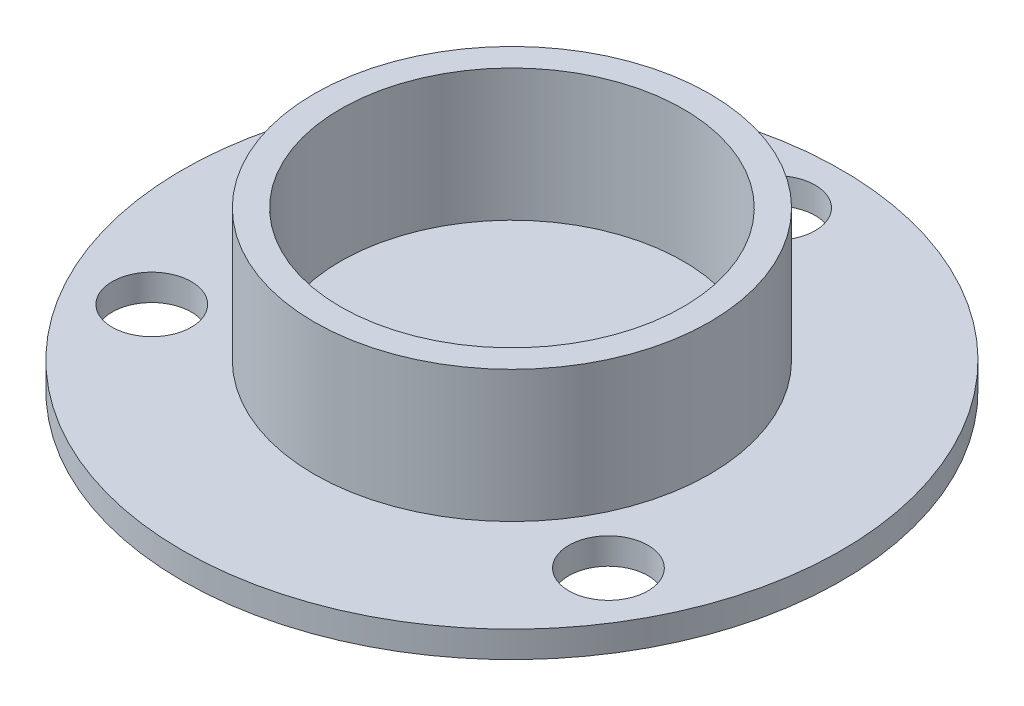
SolidWorks part; units mm, degrees
ref_plane "Front Plane" through (0, 0, 0) normal (0, 0, 1) x (1, 0, 0)
ref_plane "Top Plane" through (0, 0, 0) normal (0, 1, 0) x (1, 0, 0)
ref_plane "Right Plane" through (0, 0, 0) normal (1, 0, 0) x (0, 0, -1)
sketch "Sketch2" plane through (0, 0, 0) normal (0, 1, 0) x (1, 0, 0)
  circle A0 centre (0, 0) radius 12.5
  circle A3 centre (0, 10) radius 1.5
  circle A4 centre (8.6603, -5) radius 1.5
  circle A5 centre (-8.6603, -5) radius 1.5
  point P14 (0, 0)
  dimension "D1" = 3
  dimension "D2" = 3
extrude "Boss-Extrude1" add sketch "Sketch2" along normal blind 1
sketch "Sketch3" plane through (0, 1, 0) normal (0, 1, 0) x (1, 0, 0)
  circle A0 centre (0, 0) radius 7.5
  circle A1 centre (0, 0) radius 6.5
extrude "Boss-Extrude2" add sketch "Sketch3" along normal blind 5
